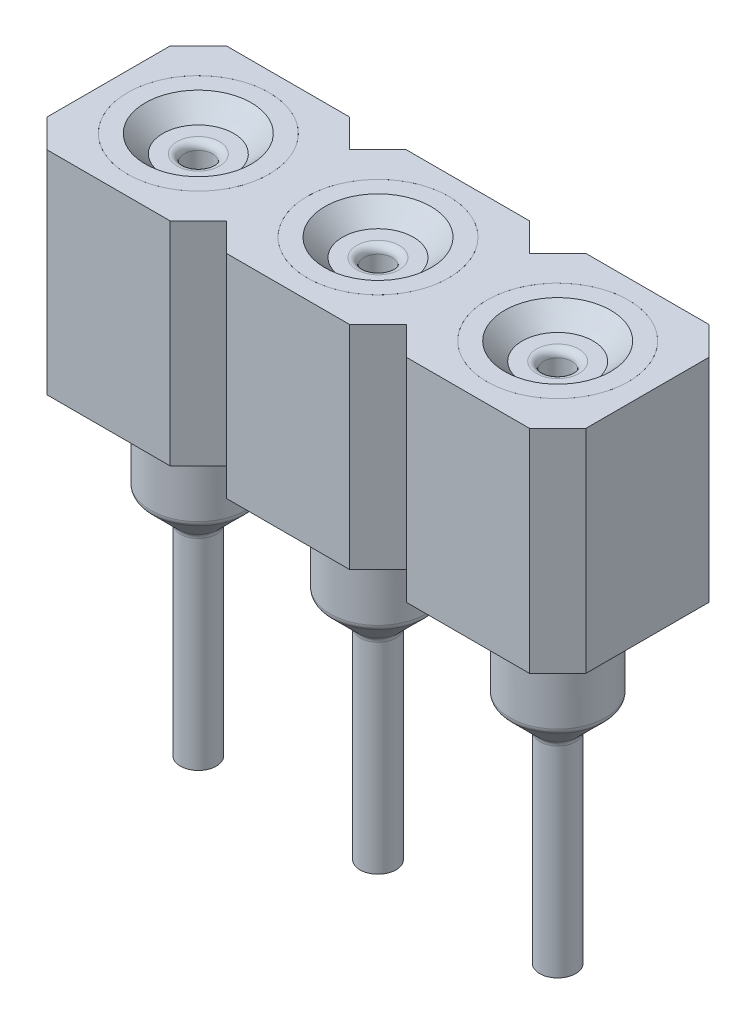
SolidWorks part; units mm, degrees
other "Plastic  Body"
other "Center Pin"
other "Right Pin"
other "Left Pin"
ref_plane "Front Plane" through (0, 0, 0) normal (0, 0, 1) x (1, 0, 0)
ref_plane "Top Plane" through (0, 0, 0) normal (0, 1, 0) x (1, 0, 0)
ref_plane "Right Plane" through (0, 0, 0) normal (1, 0, 0) x (0, 0, -1)
sketch "Sketch1" plane through (0, 0, 0) normal (0, 1, 0) x (1, 0, 0)
  line L0 (-2.54, 0) -> (2.54, 0) construction
  line L5 (2.54, 0) -> (3.81, 0) construction
  line L6 (-2.54, 0) -> (-3.81, 0) construction
  line L8 (-3.81, 1.27) -> (3.81, 1.27)
  line L9 (-3.81, 1.27) -> (-3.81, -1.27)
  line L10 (-3.81, -1.27) -> (3.81, -1.27)
  line L11 (3.81, 1.27) -> (3.81, -1.27)
  line L16 (-0.26, 0.26) -> (0.26, 0.26)
  line L17 (-0.26, 0.26) -> (-0.26, -0.26)
  line L18 (-0.26, -0.26) -> (0.26, -0.26)
  line L19 (0.26, 0.26) -> (0.26, -0.26)
  line L20 (-0.26, 0.26) -> (0.26, -0.26) construction
  line L21 (-0.26, -0.26) -> (0.26, 0.26) construction
  line L22 (2.28, -0.26) -> (2.8, -0.26)
  line L23 (2.28, -0.26) -> (2.28, 0.26)
  line L24 (2.28, 0.26) -> (2.8, 0.26)
  line L25 (2.8, -0.26) -> (2.8, 0.26)
  line L26 (2.28, -0.26) -> (2.8, 0.26) construction
  line L27 (2.28, 0.26) -> (2.8, -0.26) construction
  line L28 (-2.8, -0.26) -> (-2.28, -0.26)
  line L29 (-2.8, -0.26) -> (-2.8, 0.26)
  line L30 (-2.8, 0.26) -> (-2.28, 0.26)
  line L31 (-2.28, -0.26) -> (-2.28, 0.26)
  line L32 (-2.8, -0.26) -> (-2.28, 0.26) construction
  line L33 (-2.8, 0.26) -> (-2.28, -0.26) construction
  point P8 (0, 0)
  dimension "D1" = 5.08
  dimension "D2" = 7.62
  dimension "D3" = 2.54
  dimension "D4" = 0.52
extrude "Boss-Extrude1" add sketch "Sketch1" along normal blind 3
sketch "Sketch2" plane through (0, 0, 0) normal (0, 0, 1) x (1, 0, 0)
  line L0 (0, 3) -> (0, -4.62)
  line L1 (-3.81, 3) -> (3.81, 3) construction
  line L2 (0, 3) -> (1, 3)
  line L3 (1, 3) -> (1, 0.46)
  line L4 (1, 0.46) -> (0.675, 0.46)
  line L5 (0.675, 0.46) -> (0.675, -1.318)
  line L6 (0.675, -1.318) -> (0.254, -1.739)
  line L7 (0.254, -1.739) -> (0.254, -4.62)
  line L8 (0.254, -4.62) -> (0, -4.62)
  line L9 (0.254, -1.739) -> (0, -1.993) construction
  dimension "D1" = 2.54
  dimension "D2" = 0.675
  dimension "D3" = 7.62
  dimension "D4" = 0.254
  dimension "D5" = 45
  dimension "D6" = 4.318
  dimension "D7" = 1
revolve "Revolve1" add sketch "Sketch2" angle 360 about L0
sketch "Sketch3" plane through (0, 0, 0) normal (0, 0, 1) x (1, 0, 0)
  line L0 (0, 3) -> (0, 0)
  line L1 (0, 0) -> (0.675, 0)
  line L2 (0.675, 0.46) -> (0.675, -1.318) construction
  line L3 (-3.81, 0) -> (3.81, 0) construction
  line L4 (0.675, 0) -> (0.675, 0.46)
  line L5 (0.675, 0.46) -> (1, 0.46)
  line L6 (1, 0.46) -> (1, 3)
  line L7 (1, 3) -> (0, 3)
revolve "Cut-Revolve1" cut sketch "Sketch3" angle 360 about L0
sketch "Sketch5" plane through (0, 0, 0) normal (0, 0, 1) x (1, 0, 0)
  line L0 (0, 0) -> (0, 0.46) construction
  line L1 (-0.675, 0.46) -> (0.675, 0.46) construction
  line L2 (0, 0.46) -> (0, 3)
  line L3 (1, 3) -> (-1, 3) construction
  line L4 (0, 0.46) -> (0.2, 0.46)
  line L5 (0.2, 0.46) -> (0.2, 2.75)
  line L6 (0.2, 2.75) -> (0.5, 2.75)
  line L7 (0.5, 2.75) -> (0.75, 3)
  line L8 (0.75, 3) -> (0, 3)
  dimension "D1" = 0.2
  dimension "D2" = 0.5
  dimension "D3" = 0.75
  dimension "D4" = 45
revolve "Cut-Revolve2" cut sketch "Sketch5" angle 360 about L2
fillet "Fillet1" radius 0.1 3 edges at (0.2, 2.75, 0) (-0.254, -1.739, 0) (-0.675, -1.318, 0)
pattern_linear "LPattern1" count 2 spacing 2.54 along (1, 0, 0) count 2 spacing 2.54 along (-1, 0, 0) of "Cut-Revolve1"
pattern_linear "LPattern2" count 2 spacing 2.54 along (1, 0, 0) count 2 spacing 2.54 along (-1, 0, 0) of bodies 109 102
sketch "Sketch6" plane through (0, 3, 0) normal (0, 1, 0) x (1, 0, 0)
  line L0 (0, 0) -> (-2.54, 0) construction
  line L1 (0, 0) -> (2.54, 0) construction
  line L2 (-1.27, 0) -> (-1.27, 0.87) construction
  line L3 (-1.27, 0) -> (-1.27, -0.87) construction
  line L4 (1.27, 0) -> (1.27, 0.87) construction
  line L5 (1.27, 0) -> (1.27, -0.87) construction
  line L6 (-1.27, -0.87) -> (-1.27, -1.27) construction
  line L7 (-3.81, -1.27) -> (3.81, -1.27) construction
  line L8 (1.27, -0.87) -> (1.27, -1.27) construction
  line L9 (-1.27, 0.87) -> (-1.27, 1.27) construction
  line L10 (3.81, 1.27) -> (-3.81, 1.27) construction
  line L11 (1.27, 0.87) -> (1.27, 1.27) construction
  line L12 (-3.41, 1.27) -> (-3.81, 1.27)
  line L13 (-3.81, 1.27) -> (-3.81, 0.87)
  line L14 (-3.81, 1.27) -> (-3.81, -1.27) construction
  line L15 (-3.81, 0.87) -> (-3.41, 1.27)
  line L16 (-1.67, 1.27) -> (-0.87, 1.27)
  line L17 (-1.67, 1.27) -> (-1.27, 0.87)
  line L18 (-1.27, 0.87) -> (-0.87, 1.27)
  line L19 (0.87, 1.27) -> (1.67, 1.27)
  line L20 (-1.67, -1.27) -> (-0.87, -1.27)
  line L21 (0.87, -1.27) -> (1.67, -1.27)
  line L22 (-1.67, -1.27) -> (-1.27, -0.87)
  line L23 (-1.27, -0.87) -> (-0.87, -1.27)
  line L24 (0.87, -1.27) -> (1.27, -0.87)
  line L25 (1.27, -0.87) -> (1.67, -1.27)
  line L26 (0.87, 1.27) -> (1.27, 0.87)
  line L27 (1.27, 0.87) -> (1.67, 1.27)
  line L28 (-3.81, -0.87) -> (-3.81, -1.27)
  line L29 (-3.81, -1.27) -> (-3.41, -1.27)
  line L30 (-3.41, -1.27) -> (-3.81, -0.87)
  line L31 (3.41, 1.27) -> (3.81, 1.27)
  line L32 (3.81, 1.27) -> (3.81, 0.87)
  line L33 (3.81, -1.27) -> (3.81, 1.27) construction
  line L34 (3.81, 0.87) -> (3.41, 1.27)
  line L35 (3.81, -0.87) -> (3.81, -1.27)
  line L36 (3.81, -1.27) -> (3.41, -1.27)
  line L37 (3.41, -1.27) -> (3.81, -0.87)
  dimension "D1" = 0.4
extrude "Cut-Extrude1" cut sketch "Sketch6" against normal up to surface (3 mm away) up to face at (2.54, 0, 0.675)
